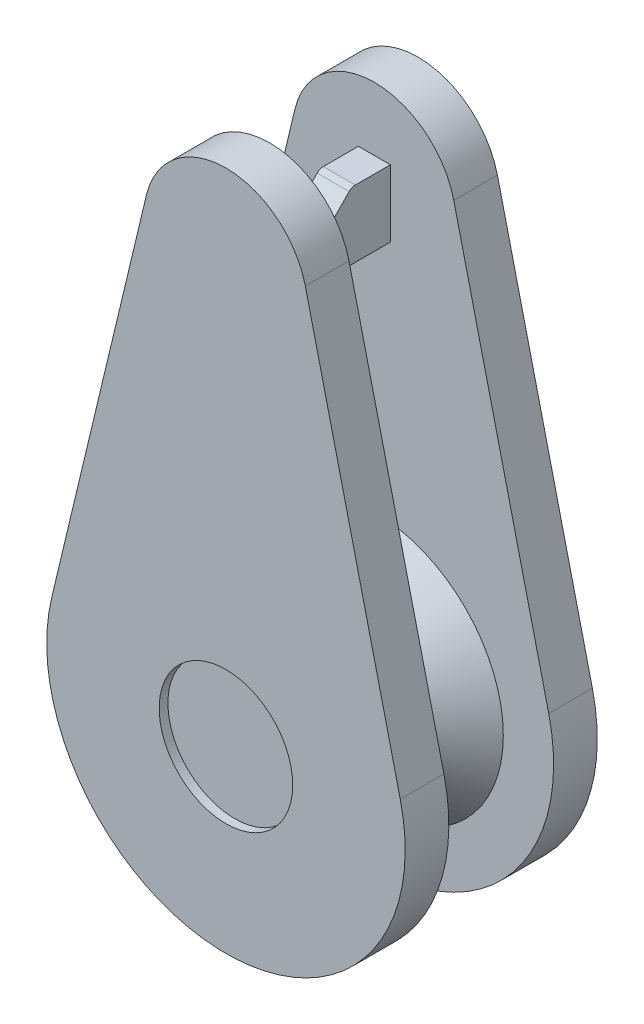
SolidWorks part; units mm, degrees
ref_plane "前视基准面" through (0, 0, 0) normal (0, 0, 1) x (1, 0, 0)
ref_plane "上视基准面" through (0, 0, 0) normal (0, 1, 0) x (1, 0, 0)
ref_plane "右视基准面" through (0, 0, 0) normal (1, 0, 0) x (0, 0, -1)
sketch "草图2" plane through (0, 0, 0) normal (0, 0, 1) x (1, 0, 0)
  line L0 (20.5077, 136.955) -> (22.6814, 146.0419)
  line L1 (26.3178, 146.0451) -> (28.4923, 136.955)
  arc A0 (20.5077, 136.955) -> (28.4923, 136.955) centre (24.5, 136) ccw
  arc A1 (22.6814, 146.0419) -> (26.3178, 146.0451) centre (24.5, 145.6069) cw
extrude "凸台-拉伸1" add sketch "草图2" along normal blind 1
sketch "草图3" plane through (0, 0, 1) normal (0, 0, 1) x (1, 0, 0)
  circle A0 centre (24.5, 136) radius 2.9527
ref_plane "基准面1" through (0, 0, 2.2) normal (0, 0, -1) x (-1, 0, 0)
sketch "草图5" plane through (0, 0, 2.2) normal (0, 0, -1) x (-1, 0, 0)
  circle A0 centre (-24.5, 136) radius 1.7382
loft "放样2" add profiles "草图3", "草图5"
sketch "草图6" plane through (0, 0, 1) normal (0, 0, 1) x (1, 0, 0)
  line L1 (24.1334, 146.0244) -> (24.8666, 146.0244)
  line L2 (24.1334, 146.0244) -> (24.1334, 144.4907)
  line L3 (24.1334, 144.4907) -> (24.8666, 144.4907)
  line L4 (24.8666, 146.0244) -> (24.8666, 144.4907)
  line L5 (24.1334, 146.0244) -> (24.8666, 144.4907) construction
  line L6 (24.1334, 144.4907) -> (24.8666, 146.0244) construction
  point P0 (24.5, 145.2576)
extrude "凸台-拉伸2" add sketch "草图6" along normal blind 2.4
sketch "草图7" plane through (24.1334, 0, 0) normal (-1, 0, 0) x (0, 0, 1)
  line L0 (1.8847, 146.0244) -> (3.4, 144.4907)
  line L1 (3.4, 146.0244) -> (1, 146.0244) construction
  line L2 (3.4, 144.4907) -> (3.4, 146.0244)
  line L3 (3.4, 146.0244) -> (1.8847, 146.0244)
extrude "切除-拉伸1" cut sketch "草图7" against normal blind 2.4
fillet "圆角1" radius 0.2 2 edges at (24.5, 144.4907, 3.4) (24.5, 146.0244, 1.8847)
mirror "镜向4" about plane through (0, 0, 2.2) normal (0, 0, -1) of "放样2", "凸台-拉伸1"
mirror "镜向5" about plane through (0, 0, 2.2) normal (0, 0, -1) of "凸台-拉伸1"
fillet "圆角2" radius 0.2 1 edges at (22.7618, 136, 2.2)
sketch "草图8" plane through (0, 0, 4.4) normal (0, 0, 1) x (1, 0, 0)
  circle A0 centre (24.5, 136) radius 1.5294
extrude "切除-拉伸3" cut sketch "草图8" against normal blind 0.2
sketch "草图9" plane through (0, 0, 0) normal (1, 0, 0) x (0, 0, -1)
  line L0 (-2.2, -4.5154) -> (-2.2, 4.5154) construction
  circle A0 centre (-2.2, 139.2511) radius 1
sketch "草图10" plane through (0, 0, 2.2) normal (0, 0, -1) x (-1, 0, 0)
  line L0 (-24.4984, 147.4768) -> (-24.5, 131.8951)
  line L1 (-24.5, 131.8951) -> (-24.4992, 139.6859)
  arc A0 (-22.6814, 146.0419) -> (-26.3178, 146.0451) centre (-24.5, 145.6069) ccw construction
  arc A1 (-28.4923, 136.955) -> (-20.5077, 136.955) centre (-24.5, 136) ccw construction
ref_plane "基准面2" through (24.5, 0, 0) normal (1, 0, 0) x (0, 0, -1)
sketch "草图11" plane through (24.5, 0, 0) normal (1, 0, 0) x (0, 0, -1)
  line L0 (-2.2, 139.2511) -> (-1.2, 139.2511)
  line L1 (-1.2, 139.2511) -> (-2.2, 140.2511)
  line L2 (-2.2, 140.2511) -> (-2.2, 139.2511)
  circle A0 centre (-2.2, 139.2511) radius 1
ref_plane "基准面3" through (20.5077, 136.955, 4.4) normal (-0.2327, -0.9726, 0) x (-0.9726, 0.2327, 0)
